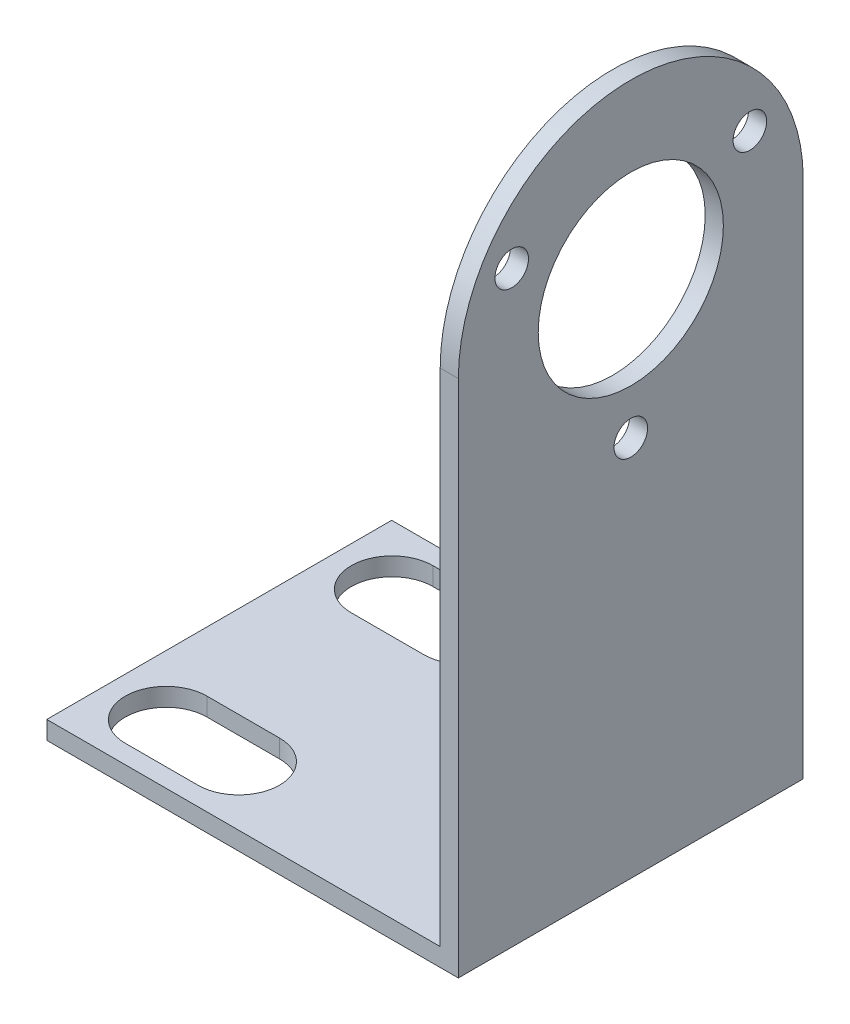
SolidWorks part; units mm, degrees
ref_plane "Front Plane" through (0, 0, 0) normal (0, 0, 1) x (1, 0, 0)
ref_plane "Top Plane" through (0, 0, 0) normal (0, 1, 0) x (1, 0, 0)
ref_plane "Right Plane" through (0, 0, 0) normal (1, 0, 0) x (0, 0, -1)
sketch "Sketch1" plane through (0, 0, 0) normal (0, 1, 0) x (1, 0, 0)
  line L1 (-45.35, 21.9763) -> (0, 21.9763)
  line L2 (-45.35, 21.9763) -> (-45.35, -16.0237)
  line L3 (-45.35, -16.0237) -> (0, -16.0237)
  line L4 (0, 21.9763) -> (0, -16.0237)
  dimension "D1" = 45.35
  dimension "D2" = 38
extrude "Boss-Extrude1" add sketch "Sketch1" along normal blind 2 contours L3 L4 L1 L2
sketch "Sketch2" plane through (0, 2, 0) normal (0, 1, 0) x (1, 0, 0)
  line L0 (-45.35, -16.0237) -> (0, -16.0237) construction
  line L1 (0, 21.9763) -> (-2, 21.9763)
  line L2 (0, 21.9763) -> (0, -16.0237)
  line L3 (0, -16.0237) -> (-2, -16.0237)
  line L4 (-2, 21.9763) -> (-2, -16.0237)
  dimension "D1" = 2
extrude "Boss-Extrude2" add sketch "Sketch2" along normal blind 74.25
sketch "Sketch3" plane through (-2, 0, 0) normal (-1, 0, 0) x (0, 0, 1)
  line L0 (-21.9763, 76.25) -> (-21.9763, 2) construction
  line L2 (-21.9763, 2) -> (16.0237, 2) construction
  line L3 (-2.9763, 57.2) -> (-2.9763, 38.9772) construction
  line L4 (-2.9763, 57.2) -> (-18.2379, 66.0113) construction
  line L5 (-2.9763, 57.2) -> (11.4539, 65.5313) construction
  circle A0 centre (-2.9763, 57.2) radius 10.2
  circle A1 centre (-16.0966, 64.775) radius 1.85
  circle A2 centre (10.144, 64.775) radius 1.85
  circle A3 centre (-2.9763, 42.05) radius 1.85
  point P8 (-16.0966, 64.775)
  point P12 (10.144, 64.775)
  point P13 (-2.9763, 42.05)
  dimension "D1" = 20.4
  dimension "D10" = 3.7
  dimension "D2" = 19
  dimension "D4" = 55.2
  dimension "D5" = 120
  dimension "D6" = 120
  dimension "D7" = 15.15
  dimension "D8" = 15.15
  dimension "D9" = 15.15
extrude "Cut-Extrude1" cut sketch "Sketch3" against normal blind 50
sketch "Sketch14" plane through (0, 0, 0) normal (1, 0, 0) x (0, 0, -1)
  line L0 (-16.0237, 57.2) -> (-16.0237, 90.2824)
  line L1 (-16.0237, 90.2824) -> (21.9763, 90.2824)
  line L2 (21.9763, 90.2824) -> (21.9763, 57.2)
  arc A0 (21.9763, 57.2) -> (-16.0237, 57.2) centre (2.9763, 57.2) ccw
extrude "Cut-Extrude2" cut sketch "Sketch14" against normal through all
sketch "Sketch15" plane through (0, 2, 0) normal (0, 1, 0) x (1, 0, 0)
  line L0 (-30.75, -9.4737) -> (-38.75, -9.4737) construction
  line L1 (-30.75, -13.9737) -> (-38.75, -13.9737)
  line L2 (-30.75, -4.9737) -> (-38.75, -4.9737)
  line L3 (-45.35, 2.9763) -> (-12.9145, 2.9763) construction
  line L6 (-45.35, 21.9763) -> (-45.35, -16.0237) construction
  line L7 (-45.35, -16.0237) -> (0, -16.0237) construction
  line L8 (-30.75, 15.4263) -> (-38.75, 15.4263) construction
  line L9 (-30.75, 19.9263) -> (-38.75, 19.9263)
  line L10 (-30.75, 10.9263) -> (-38.75, 10.9263)
  arc A0 (-30.75, -13.9737) -> (-30.75, -4.9737) centre (-30.75, -9.4737) ccw
  arc A1 (-38.75, -4.9737) -> (-38.75, -13.9737) centre (-38.75, -9.4737) ccw
  arc A4 (-30.75, 19.9263) -> (-30.75, 10.9263) centre (-30.75, 15.4263) cw
  arc A5 (-38.75, 10.9263) -> (-38.75, 19.9263) centre (-38.75, 15.4263) cw
  point P2 (-34.75, -9.4737)
  point P11 (-34.75, 15.4263)
  dimension "D2" = 8
  dimension "D1" = 9
  dimension "D3" = 10.6
  dimension "D4" = 6.55
extrude "Cut-Extrude3" cut sketch "Sketch15" against normal through all
sketch "Sketch16" plane through (0, 0, 0) normal (1, 0, 0) x (0, 0, -1)
  circle A0 centre (-58.8906, 3.2732) radius 96.9822 construction
  dimension "D1" = 193.9644
